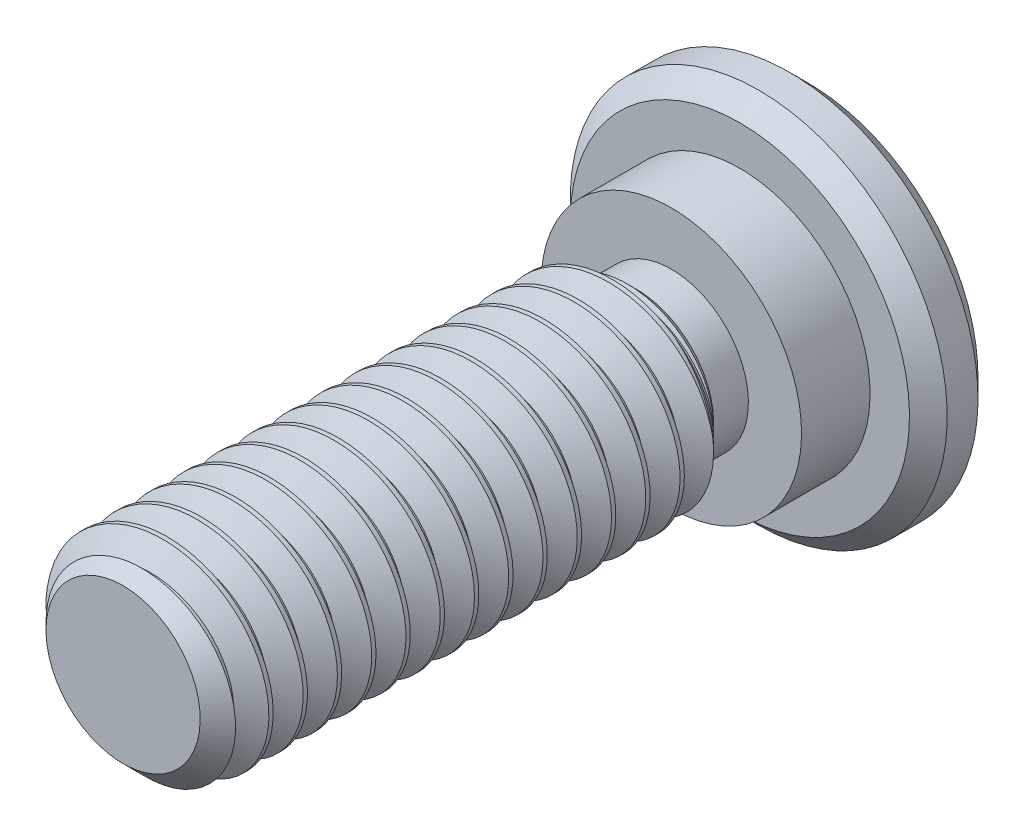
SolidWorks part; units mm, degrees
other "DetailItem1"
ref_plane "Front Plane" through (0, 0, 0) normal (0, 0, 1) x (1, 0, 0)
ref_plane "Top Plane" through (0, 0, 0) normal (0, 1, 0) x (1, 0, 0)
ref_plane "Right Plane" through (0, 0, 0) normal (1, 0, 0) x (0, 0, -1)
sketch "Sketch1" plane through (0, 0, 0) normal (1, 0, 0) x (0, 0, -1)
  line L0 (0, 0) -> (-9, 0) construction
  line L1 (0, 0) -> (1, 0) construction
  line L2 (1, 2.75) -> (1, -2.75) construction
  line L3 (-9, 1.5) -> (-9, -1.5) construction
  line L4 (0, 1.9) -> (0, -1.9) construction
  line L5 (-9, 1.5) -> (-8.5, 1.5) construction
  line L6 (1, 1) -> (1, -1) construction
  line L7 (0, 1.9) -> (-1, 1.9) construction
  line L8 (-1, 1.9) -> (-1, 1.125) construction
  line L9 (-1, 1.125) -> (-1.508, 1.125) construction
  line L10 (-1.508, 1.125) -> (-1.883, 1.5) construction
  point P2 (-7.25, -1.5)
  point P4 (-1, 0)
  point P8 (1, 0)
  point P11 (-9, 0)
  point P14 (0, 0)
  point P19 (1, 0)
  dimension "Thread Diameter" = 3
  dimension "Head Diameter" = 5.5
  dimension "Head Height" = 1
  dimension "Shoulder Diameter" = 3.8
  dimension "Shoulder Length" = 1
  dimension "Thread Pitch" = 0.5
  dimension "Drive Size" = 2
  dimension "D1" = 1.75
  dimension "D2" = 45
  dimension "Undercut Length" = 0.508
  dimension "D3" = 2.25
  dimension "Length" = 8
sketch "Sketch13" plane through (0, 0, 0) normal (1, 0, 0) x (0, 0, -1)
  line L0 (1, 2.75) -> (0, 2.75)
  line L1 (0, 2.75) -> (0, 1.9)
  line L3 (-9, 1.5) -> (-9, 0)
  line L4 (-9, 0) -> (1, 0)
  line L5 (1, 0) -> (1, 2.75)
  line L6 (-1.508, 1.125) -> (-1.883, 1.5) construction
  line L7 (-1, 1.125) -> (-1.508, 1.125) construction
  line L8 (-1, 1.9) -> (-1, 1.125) construction
  line L9 (0, 1.9) -> (-1, 1.9) construction
  line L10 (-1.508, 1.125) -> (-1.883, 1.5)
  line L11 (-1, 1.125) -> (-1.508, 1.125)
  line L12 (-1, 1.9) -> (-1, 1.125)
  line L13 (0, 1.9) -> (-1, 1.9)
  line L14 (-1.883, 1.5) -> (-9, 1.5)
revolve "Revolve1" add sketch "Sketch13" angle 360 about L4
sketch "Sketch2" plane through (0, 0, 9) normal (0, 0, 1) x (1, 0, 0)
  circle A2 centre (0, 0) radius 1.5
chamfer "Chamfer2" distance 0.375 angle 45 1 edges at (0, -1.5, 9)
sketch "Sketch3" plane through (0, 0, 0) normal (1, 0, 0) x (0, 0, -1)
  line L0 (-8.9687, 1.5541) -> (-9.4687, 1.5541) construction
  line L1 (-9.4687, 1.5541) -> (-9.2187, 1.1211) construction
  line L2 (-9.2187, 1.1211) -> (-8.9687, 1.5541) construction
  line L4 (-9, 1.5) -> (-9.4375, 1.5) construction
  line L5 (-9.2187, 1.5541) -> (-9.2187, 1.5) construction
  line L6 (-9.4531, 1.5271) -> (-8.9844, 1.5271)
  line L7 (-8.9844, 1.5271) -> (-9.4531, 1.5271) construction
  line L8 (-9.1875, 1.1752) -> (-9.25, 1.1752) construction
  line L9 (-9.2187, 1.1752) -> (-9.2187, 1.1211) construction
  line L10 (-8.9844, 1.5271) -> (-9.1875, 1.1752)
  line L11 (-9.1875, 1.1752) -> (-9.25, 1.1752)
  line L12 (-9.25, 1.1752) -> (-9.4531, 1.5271)
  point P16 (-9.2187, 1.5271)
  dimension "D1" = 0.5
  dimension "D2" = 0.0625
sketch "Sketch7" plane through (0, 0, -1) normal (0, 0, -1) x (-1, 0, 0)
  line L1 (0, 1.1547) -> (-1, 0.5774)
  line L2 (-1, 0.5774) -> (-1, -0.5774)
  line L3 (-1, -0.5774) -> (0, -1.1547)
  line L4 (0, -1.1547) -> (1, -0.5774)
  line L5 (1, -0.5774) -> (1, 0.5774)
  line L6 (1, 0.5774) -> (0, 1.1547)
  circle A0 centre (0, 0) radius 1 construction
extrude "Cut-Extrude1" cut sketch "Sketch7" against normal blind 1.5
chamfer "Chamfer1" distance 0.275 angle 45 2 edges at (0, -2.75, -1) (0, -2.75, 0)
sketch "Sketch8" plane through (0, 0, -1) normal (0, 0, -1) x (-1, 0, 0)
  circle A0 centre (0, 0) radius 1.1547
extrude "Cut-Extrude2" cut sketch "Sketch8" against normal through all draft 45
curve "Helix/Spiral1" pitch 0.5 height 7.9 turns 15.8 parameters "pitch"=0.5
sweep "Cut-Sweep1" cut profiles "Sketch3" path "Helix/Spiral1"
equation "\"D3@Helix/Spiral1\"=\"Length@Sketch1\"-.1"
equation "\"D1@Cut-Extrude1\" = \"Drive Size@Sketch1\" * .75"
equation "\"D1@Chamfer1\" = \"Head Diameter@Sketch1\" * .05"
equation "\"D1@Chamfer2\"=\"pitch@Helix/Spiral1\"*.750"
equation "\"D1@Sketch3\" = \"Thread Pitch@Sketch1\""
equation "\"D2@Sketch3\"=\"D1@Sketch3\"/ 1/8"
equation "\"pitch@Helix/Spiral1\" = \"Thread Pitch@Sketch1\""
equation "\"D1@Sketch1\" = \"Thread Pitch@Sketch1\" * 3.5"
equation "\"D3@Sketch1\"=\"Thread Diameter@Sketch1\"-(\"Thread Pitch@Sketch1\"*1.5)"
